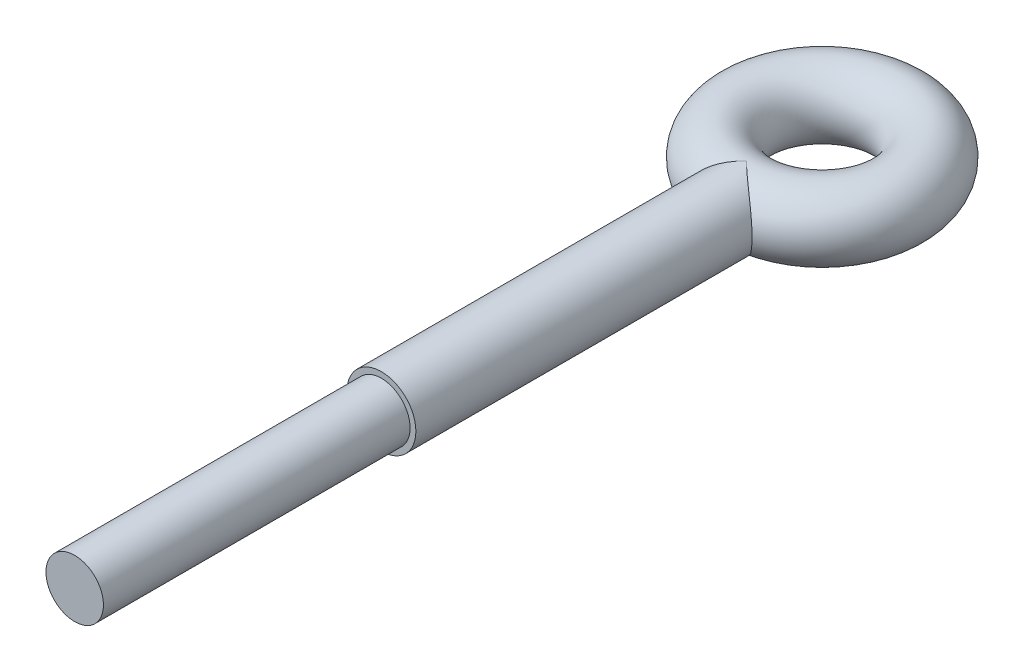
SolidWorks part; units mm, degrees
ref_plane "前视基准面" through (0, 0, 0) normal (0, 0, 1) x (1, 0, 0)
ref_plane "上视基准面" through (0, 0, 0) normal (0, 1, 0) x (1, 0, 0)
ref_plane "右视基准面" through (0, 0, 0) normal (1, 0, 0) x (0, 0, -1)
sketch "草图1" plane through (0, 0, 0) normal (0, 0, 1) x (1, 0, 0)
  line L0 (0, 9.6598) -> (0, -10.0493) construction
  circle A2 centre (-3.95, 0) radius 1.8
  dimension "D1" = 3.6
  dimension "D2" = 3.95
revolve "旋转1" add sketch "草图1" angle 360 about L0
ref_plane "基准面1" through (0, 0, 23) normal (0, 0, 1) x (1, 0, 0)
sketch "草图2" plane through (0, 0, 23) normal (0, 0, 1) x (1, 0, 0)
  circle A0 centre (0, 0) radius 1.8
extrude "凸台-拉伸1" add sketch "草图2" against normal up to surface (17.539 mm away)
sketch "草图3" plane through (0, 0, 23) normal (0, 0, 1) x (1, 0, 0)
  circle A0 centre (0, 0) radius 1.5
  dimension "D1" = 3
extrude "凸台-拉伸2" add sketch "草图3" along normal blind 16
sketch "草图8" plane through (0, 0, 0) normal (0, 1, 0) x (1, 0, 0)
  circle A0 centre (0, 0) radius 1
